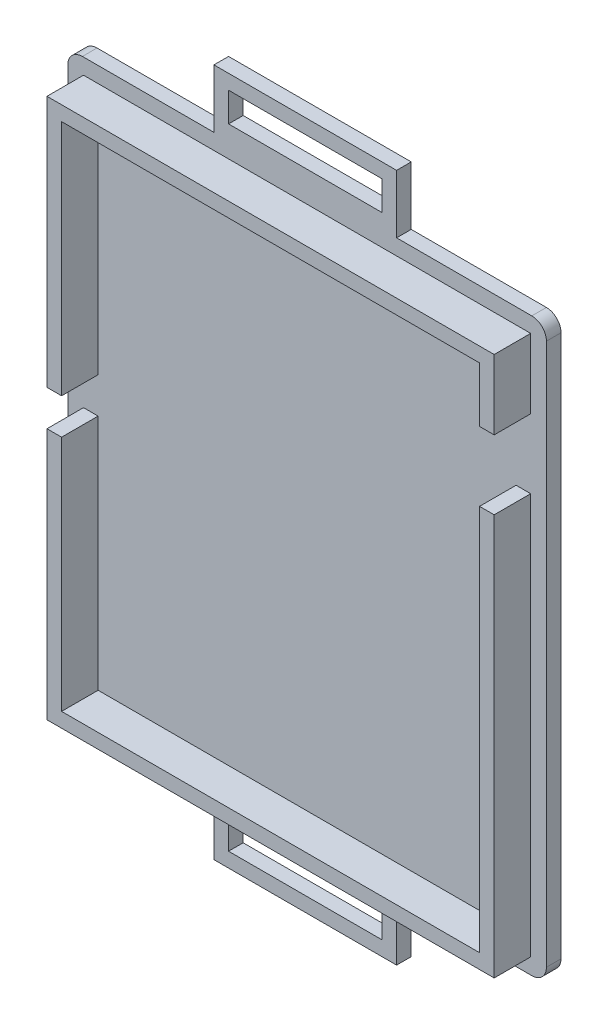
SolidWorks part; units mm, degrees
ref_plane "Front Plane" through (0, 0, 0) normal (0, 0, 1) x (1, 0, 0)
ref_plane "Top Plane" through (0, 0, 0) normal (0, 1, 0) x (1, 0, 0)
ref_plane "Right Plane" through (0, 0, 0) normal (1, 0, 0) x (0, 0, -1)
sketch "Sketch1" plane through (0, 0, 0) normal (0, 0, 1) x (1, 0, 0)
  line L1 (-28.7385, 31.664) -> (36.7615, 31.664)
  line L2 (-28.7385, 31.664) -> (-28.7385, -46.536)
  line L3 (-28.7385, -46.536) -> (36.7615, -46.536)
  line L4 (36.7615, 31.664) -> (36.7615, -46.536)
  dimension "D1" = 65.5
  dimension "D2" = 78.2
extrude "Boss-Extrude1" add sketch "Sketch1" along normal blind 2
sketch "Sketch2" plane through (0, 0, 2) normal (0, 0, 1) x (1, 0, 0)
  line L0 (36.7615, 31.664) -> (-28.7385, 31.664) construction
  line L1 (-26.5885, 29.514) -> (34.6115, 29.514)
  line L2 (-26.5885, 29.514) -> (-26.5885, -44.386)
  line L3 (-26.5885, -44.386) -> (34.6115, -44.386)
  line L4 (34.6115, 29.514) -> (34.6115, -44.386)
  line L5 (-24.5885, 27.514) -> (32.6115, 27.514)
  line L6 (-24.5885, 27.514) -> (-24.5885, -42.386)
  line L7 (-24.5885, -42.386) -> (32.6115, -42.386)
  line L8 (32.6115, 27.514) -> (32.6115, -42.386)
  line L9 (-28.7385, 31.664) -> (-28.7385, -46.536) construction
  line L10 (36.7615, -46.536) -> (36.7615, 31.664) construction
  line L11 (-28.7385, -46.536) -> (36.7615, -46.536) construction
  dimension "D1" = 2.15
  dimension "D2" = 2.15
  dimension "D3" = 2.15
  dimension "D4" = 2
  dimension "D5" = 2
  dimension "D6" = 2
  dimension "D7" = 2
extrude "Boss-Extrude2" add sketch "Sketch2" along normal blind 5
sketch "Sketch3" plane through (34.6115, 0, 0) normal (1, 0, 0) x (0, 0, -1)
  line L0 (-7, -44.386) -> (-7, 29.514) construction
  line L5 (-2, -44.386) -> (-2, 29.514) construction
  line L7 (-7, 29.514) -> (-2, 29.514) construction
  line L8 (-7, 19.984) -> (-2, 19.984)
  line L9 (-7, 19.984) -> (-7, 10.514)
  line L10 (-7, 10.514) -> (-2, 10.514)
  line L11 (-2, 19.984) -> (-2, 10.514)
  dimension "D3" = 9.53
  dimension "D4" = 19
extrude "Cut-Extrude1" cut sketch "Sketch3" against normal up to surface (2 mm away) up to face at (32.6115, -7.436, 4.5)
sketch "Sketch4" plane through (-26.5885, 0, 0) normal (-1, 0, 0) x (0, 0, 1)
  line L0 (2, 29.514) -> (2, -44.386) construction
  line L1 (2, -4.986) -> (7, -4.986)
  line L2 (2, -4.986) -> (2, -9.886)
  line L3 (2, -9.886) -> (7, -9.886)
  line L4 (7, -4.986) -> (7, -9.886)
  line L5 (7, 29.514) -> (7, -44.386) construction
  line L6 (7, 29.514) -> (2, 29.514) construction
  line L7 (7, -44.386) -> (2, -44.386) construction
  dimension "D1" = 34.5
  dimension "D2" = 34.5
extrude "Cut-Extrude2" cut sketch "Sketch4" against normal up to surface (2 mm away) up to face at (-24.5885, -7.436, 4.5)
fillet "Fillet1" radius 2 4 edges at (-28.7385, -46.536, 1) (-28.7385, 31.664, 1) (36.7615, 31.664, 1) (36.7615, -46.536, 1)
sketch "Sketch5" plane through (0, 31.664, 0) normal (0, 1, 0) x (1, 0, 0)
  line L0 (34.7615, 0) -> (-26.7385, 0) construction
  line L1 (-8.7385, 0) -> (16.2615, 0)
  line L2 (-8.7385, 0) -> (-8.7385, -2)
  line L3 (-8.7385, -2) -> (16.2615, -2)
  line L4 (16.2615, 0) -> (16.2615, -2)
  line L5 (34.6115, -2) -> (-26.5885, -2) construction
  line L6 (-28.7385, -2) -> (-28.7385, 0) construction
  dimension "D1" = 20
  dimension "D2" = 25
extrude "Boss-Extrude3" add sketch "Sketch5" along normal blind 8
sketch "Sketch6" plane through (0, -46.536, 0) normal (0, -1, 0) x (1, 0, 0)
  line L0 (-26.7385, 0) -> (34.7615, 0) construction
  line L1 (-8.7385, 0) -> (16.2615, 0)
  line L2 (-8.7385, 0) -> (-8.7385, 2)
  line L3 (-8.7385, 2) -> (16.2615, 2)
  line L4 (16.2615, 0) -> (16.2615, 2)
  line L5 (-26.7385, 2) -> (34.7615, 2) construction
  line L6 (-28.7385, 0) -> (-28.7385, 2) construction
  dimension "D1" = 20
  dimension "D2" = 25
extrude "Boss-Extrude4" add sketch "Sketch6" along normal blind 8
sketch "Sketch7" plane through (0, 0, 2) normal (0, 0, 1) x (1, 0, 0)
  line L0 (-8.7385, 39.664) -> (16.2615, 39.664) construction
  line L1 (-6.7385, -52.536) -> (14.2615, -52.536)
  line L2 (-6.7385, -52.536) -> (-6.7385, -48.536)
  line L3 (-6.7385, -48.536) -> (14.2615, -48.536)
  line L4 (14.2615, -52.536) -> (14.2615, -48.536)
  line L5 (-6.7385, 33.664) -> (14.2615, 33.664)
  line L6 (-6.7385, 33.664) -> (-6.7385, 37.664)
  line L7 (-6.7385, 37.664) -> (14.2615, 37.664)
  line L8 (14.2615, 33.664) -> (14.2615, 37.664)
  line L9 (16.2615, 39.664) -> (16.2615, 31.664) construction
  line L10 (-8.7385, 39.664) -> (-8.7385, 31.664) construction
  line L11 (-8.7385, 31.664) -> (-26.7385, 31.664) construction
  line L12 (16.2615, -54.536) -> (-8.7385, -54.536) construction
  line L13 (16.2615, -54.536) -> (16.2615, -46.536) construction
  line L14 (-8.7385, -54.536) -> (-8.7385, -46.536) construction
  line L15 (16.2615, -46.536) -> (34.7615, -46.536) construction
  dimension "D1" = 2
  dimension "D2" = 2
  dimension "D3" = 2
  dimension "D4" = 2
  dimension "D5" = 2
  dimension "D6" = 2
  dimension "D7" = 2
extrude "Cut-Extrude3" cut sketch "Sketch7" against normal through all
equation "\"W\"=4.06295"
